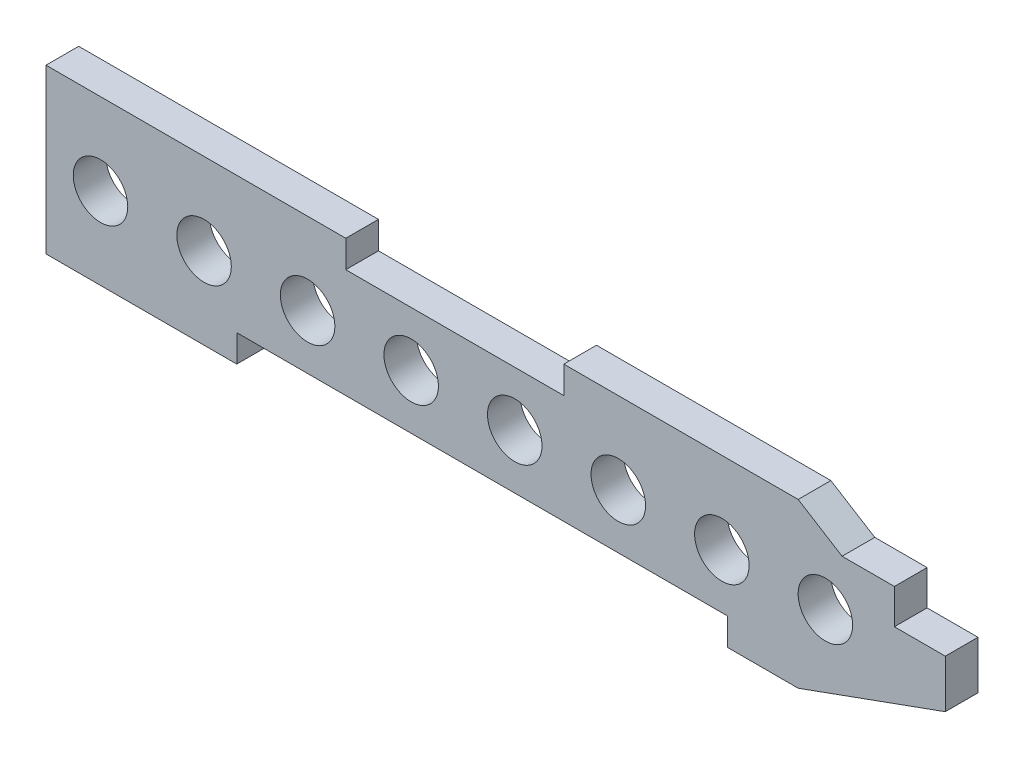
SolidWorks part; units mm, degrees
ref_plane "Front Plane" through (0, 0, 0) normal (0, 0, 1) x (1, 0, 0)
ref_plane "Top Plane" through (0, 0, 0) normal (0, 1, 0) x (1, 0, 0)
ref_plane "Right Plane" through (0, 0, 0) normal (1, 0, 0) x (0, 0, -1)
sketch "Sketch1" plane through (0, 0, 0) normal (0, 0, 1) x (1, 0, 0)
  line L0 (-197.803, 35.8758) -> (-197.803, -24.1242)
  line L1 (-197.803, -24.1242) -> (-127.803, -24.1242)
  line L2 (-127.803, -24.1242) -> (-127.803, -14.1242)
  line L3 (-127.803, -14.1242) -> (52.197, -14.1242)
  line L4 (52.197, -14.1242) -> (52.197, -24.1242)
  line L5 (52.197, -24.1242) -> (78.207, -24.1242)
  line L6 (78.207, -24.1242) -> (132.197, -4.5942)
  line L7 (132.197, -4.5942) -> (132.197, 13.0658)
  line L8 (132.197, 13.0658) -> (113.517, 13.0658)
  line L9 (113.517, 13.0658) -> (113.517, 25.8758)
  line L10 (113.517, 25.8758) -> (94.317, 25.8758)
  line L11 (94.317, 25.8758) -> (78.207, 35.8758)
  line L12 (78.207, 35.8758) -> (-7.803, 35.8758)
  line L13 (-7.803, 35.8758) -> (-7.803, 25.8758)
  line L14 (-7.803, 25.8758) -> (-87.803, 25.8758)
  line L15 (-87.803, 25.8758) -> (-87.803, 35.8758)
  line L16 (-87.803, 35.8758) -> (-197.803, 35.8758)
  line L17 (-197.803, 5.8758) -> (-300.1081, 5.8758) construction
  line L18 (-300.1081, 5.8758) -> (181.2478, 5.8758) construction
  line L19 (-177.803, 5.8758) -> (-139.803, 5.8758) construction
  circle A0 centre (-177.803, 5.8758) radius 10
  circle A1 centre (-139.803, 5.8758) radius 10
  circle A2 centre (-101.803, 5.8758) radius 10
  circle A3 centre (-63.803, 5.8758) radius 10
  circle A4 centre (-25.803, 5.8758) radius 10
  circle A5 centre (12.197, 5.8758) radius 10
  circle A6 centre (50.197, 5.8758) radius 10
  circle A7 centre (88.197, 5.8758) radius 10
  dimension "D16" = 20
  dimension "D17" = 20
  dimension "D1" = 60
  dimension "D2" = 19.53
  dimension "D3" = 110
  dimension "D4" = 12.81
  dimension "D5" = 37.19
  dimension "D6" = 18.68
  dimension "D7" = 330
  dimension "D8" = 70
  dimension "D9" = 180
  dimension "D10" = 53.99
  dimension "D11" = 80
  dimension "D12" = 10
  dimension "D13" = 10
  dimension "D14" = 53.99
  dimension "D15" = 37.88
  dimension "D18" = 30
  dimension "D19" = 38
  dimension "D20" = 266
extrude "Boss-Extrude3" add sketch "Sketch1" along normal blind 12
